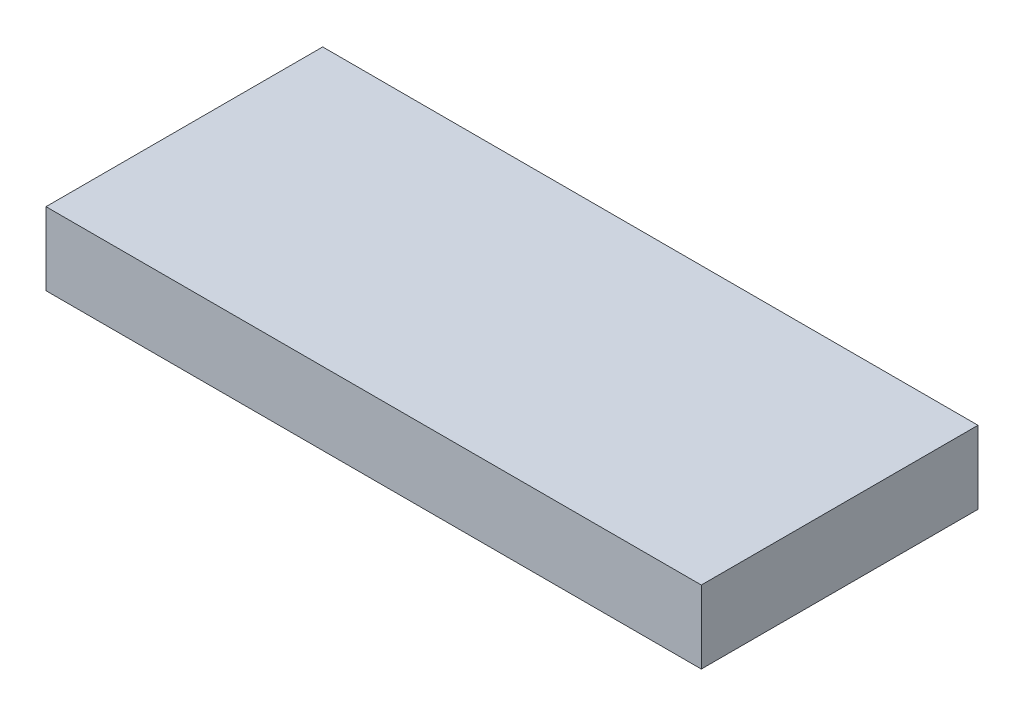
SolidWorks part; units mm, degrees
ref_plane "Front Plane" through (0, 0, 0) normal (0, 0, 1) x (1, 0, 0)
ref_plane "Top Plane" through (0, 0, 0) normal (0, 1, 0) x (1, 0, 0)
ref_plane "Right Plane" through (0, 0, 0) normal (1, 0, 0) x (0, 0, -1)
sketch "Sketch1" plane through (0, 0, 0) normal (0, 1, 0) x (1, 0, 0)
  line L1 (0, 0) -> (57.15, 0)
  line L2 (0, 0) -> (0, -24.13)
  line L3 (0, -24.13) -> (57.15, -24.13)
  line L4 (57.15, 0) -> (57.15, -24.13)
  dimension "D1" = 57.15
  dimension "D2" = 24.13
extrude "Boss-Extrude1" add sketch "Sketch1" along normal blind 6.35
